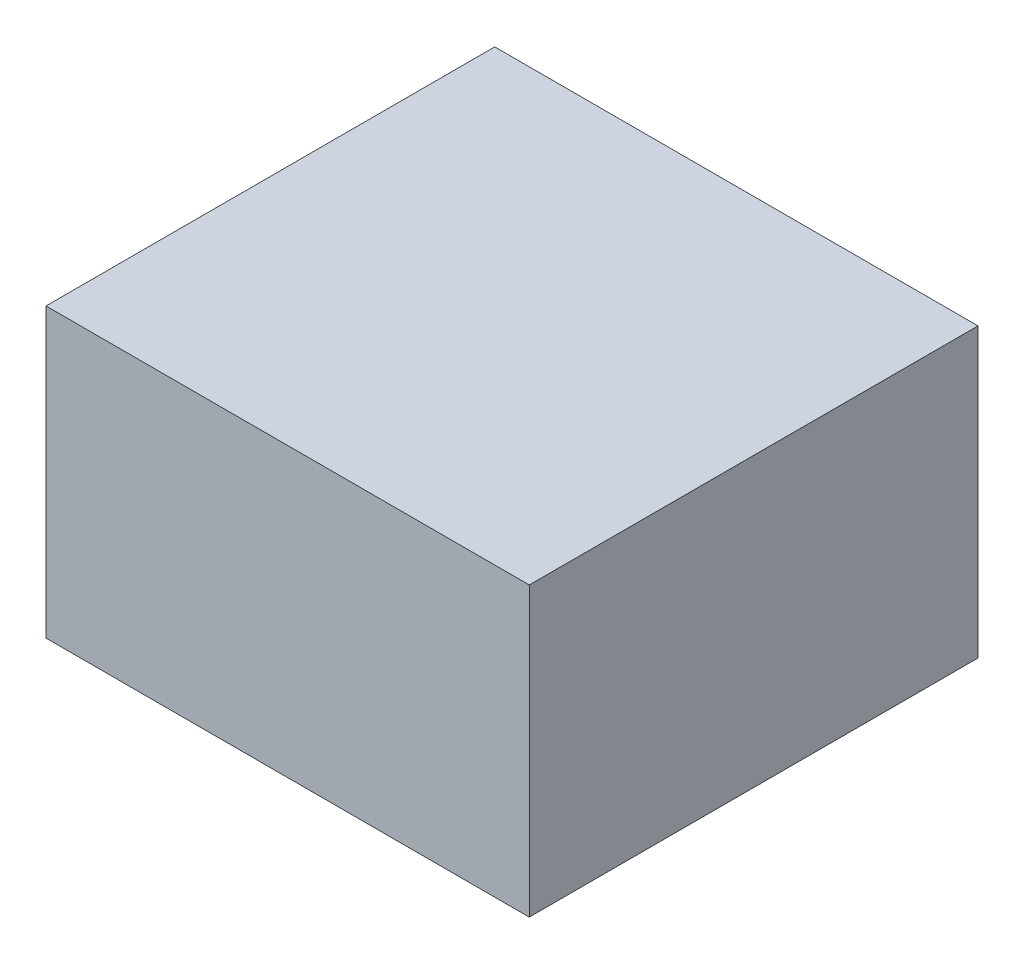
SolidWorks part; units mm, degrees
ref_plane "Front Plane" through (0, 0, 0) normal (0, 0, 1) x (1, 0, 0)
ref_plane "Top Plane" through (0, 0, 0) normal (0, 1, 0) x (1, 0, 0)
ref_plane "Right Plane" through (0, 0, 0) normal (1, 0, 0) x (0, 0, -1)
sketch "Sketch1" plane through (0, 0, 0) normal (0, 1, 0) x (1, 0, 0)
  line L1 (0, 0) -> (84, 0)
  line L2 (0, 0) -> (0, 78)
  line L3 (0, 78) -> (84, 78)
  line L4 (84, 0) -> (84, 78)
  dimension "D1" = 78
  dimension "D2" = 84
extrude "Boss-Extrude1" add sketch "Sketch1" along normal blind 50
